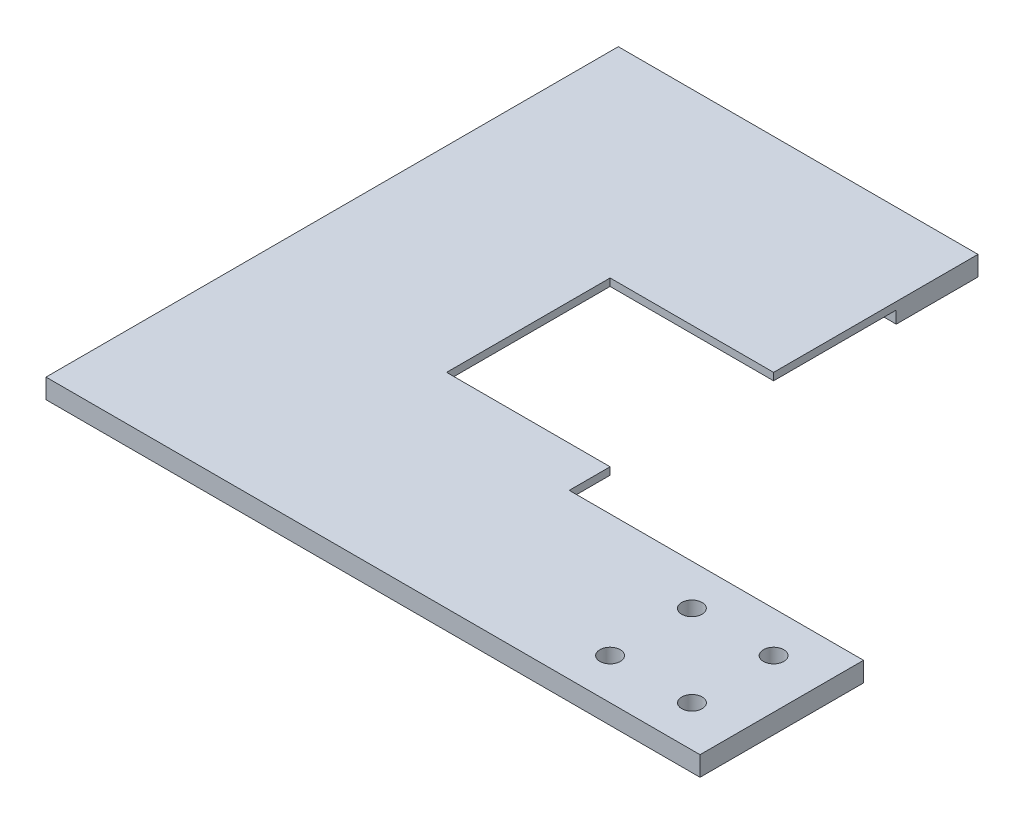
SolidWorks part; units mm, degrees
material "6061-T4 (SS)"
ref_plane "Front Plane" through (0, 0, 0) normal (0, 0, 1) x (1, 0, 0)
ref_plane "Top Plane" through (0, 0, 0) normal (0, 1, 0) x (1, 0, 0)
ref_plane "Right Plane" through (0, 0, 0) normal (1, 0, 0) x (0, 0, -1)
sketch "Sketch1" plane through (0, 0, 0) normal (0, 1, 0) x (1, 0, 0)
  line L0 (0, 50.8) -> (-91.44, 50.8)
  line L1 (0, 0) -> (-203.2, 0)
  line L2 (0, 0) -> (0, 50.8)
  line L3 (-91.44, 177.8) -> (-203.2, 177.8)
  line L4 (-203.2, 0) -> (-203.2, 177.8)
  line L7 (-142.24, 114.3) -> (-91.44, 114.3)
  line L8 (-142.24, 114.3) -> (-142.24, 63.5)
  line L9 (-142.24, 63.5) -> (-91.44, 63.5)
  line L10 (-91.44, 114.3) -> (-91.44, 177.8)
  line L12 (-91.44, 50.8) -> (-91.44, 63.5)
  circle A0 centre (-15.24, 38.1) radius 3.175
  circle A1 centre (-40.64, 38.1) radius 3.175
  circle A2 centre (-40.64, 12.7) radius 3.175
  circle A3 centre (-15.2008, 12.7) radius 3.175
  point P17 (-116.84, 88.9)
  dimension "D3" = 15.24
  dimension "D4" = 15.2008
  dimension "D5" = 40.64
  dimension "D6" = 40.64
  dimension "D7" = 12.7
  dimension "D9" = 12.7
  dimension "D11" = 6.35
  dimension "D12" = 6.35
  dimension "D13" = 6.35
  dimension "D14" = 6.35
  dimension "D2" = 203.2
  dimension "D8" = 38.1
  dimension "D10" = 38.1
  dimension "D15" = 50.8
  dimension "D16" = 177.8
  dimension "D18" = 116.84
  dimension "D19" = 88.9
  dimension "D20" = 50.8
  dimension "D21" = 50.8
  dimension "D22" = 25.4
  dimension "D23" = 25.4
extrude "Boss-Extrude1" add sketch "Sketch1" against normal blind 6.096
sketch "Sketch2" plane through (0, -6.096, 0) normal (0, -1, 0) x (1, 0, 0)
  line L1 (-190.5, -12.7) -> (-99.06, -12.7)
  line L2 (-190.5, -12.7) -> (-190.5, -165.1)
  line L3 (-190.5, -165.1) -> (-99.06, -165.1)
  line L4 (-99.06, -12.7) -> (-99.06, -165.1)
  line L5 (0, 0) -> (-203.2, 0) construction
  line L6 (-91.44, -177.8) -> (-203.2, -177.8) construction
  line L7 (-203.2, 0) -> (-203.2, -177.8) construction
  line L8 (-91.44, -50.8) -> (-91.44, -63.5) construction
  dimension "D1" = 12.7
  dimension "D2" = 12.7
  dimension "D3" = 12.7
  dimension "D4" = 7.62
sketch "Sketch3" plane through (0, -6.096, 0) normal (0, -1, 0) x (1, 0, 0)
  line L0 (-91.44, -50.8) -> (-94.0605, -50.8)
  line L1 (-177.8, -25.4) -> (-94.0605, -25.4)
  line L2 (-177.8, -25.4) -> (-177.8, -152.4)
  line L3 (-177.8, -152.4) -> (-91.44, -152.4)
  line L4 (-94.0605, -25.4) -> (-94.0605, -50.8)
  line L5 (-91.44, -114.3) -> (-91.44, -177.8) construction
  line L6 (-91.44, -50.8) -> (-91.44, -152.4)
  dimension "D1" = 63.5
  dimension "D2" = 63.5
  dimension "D3" = 60.96
extrude "Cut-Extrude1" cut sketch "Sketch2" against normal blind 1.27
extrude "Cut-Extrude2" cut sketch "Sketch3" against normal blind 3.81
